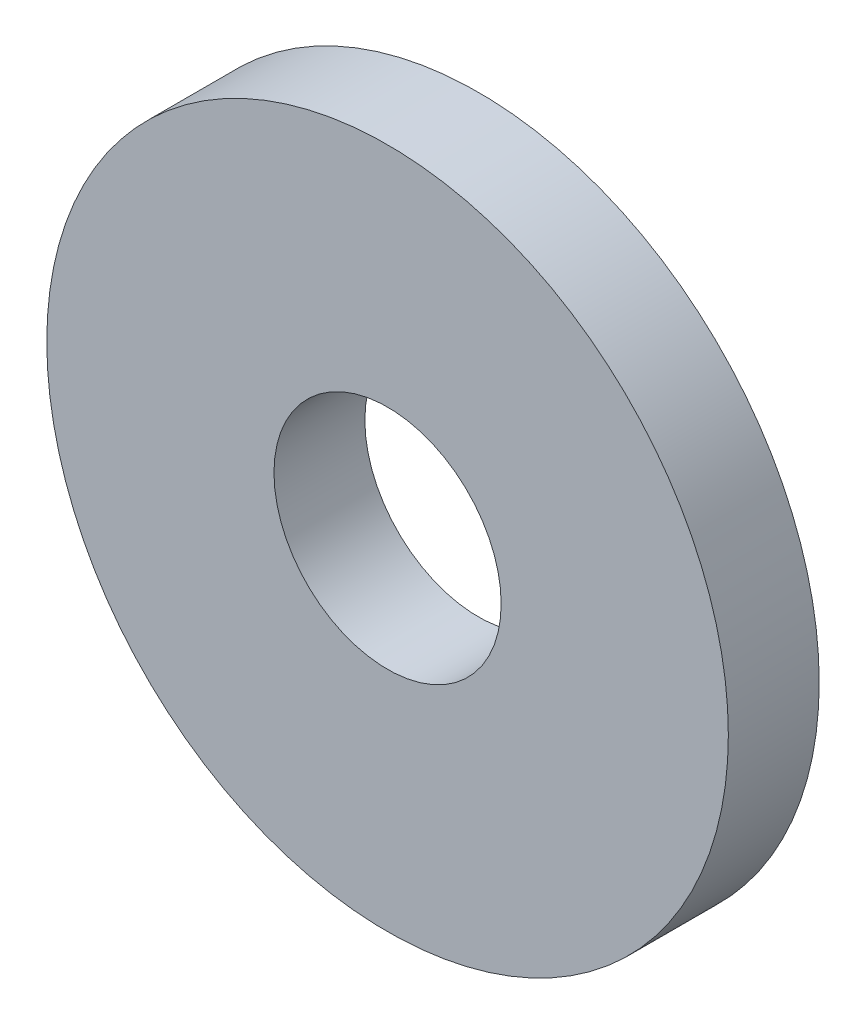
SolidWorks part; units mm, degrees
ref_plane "Front" through (0, 0, 0) normal (0, 0, 1) x (1, 0, 0)
ref_plane "Top" through (0, 0, 0) normal (0, 1, 0) x (1, 0, 0)
ref_plane "Right" through (0, 0, 0) normal (1, 0, 0) x (0, 0, -1)
sketch "Sketch1" plane through (0, 0, 0) normal (0, 0, 1) x (1, 0, 0)
  circle A0 centre (0, 0) radius 2.5
  circle A1 centre (0, 0) radius 7.5
  circle A2 centre (0, 0) radius 2.5 construction
  dimension "D1" = 5
extrude "Boss-Extrude1" add sketch "Sketch1" along normal blind 2
